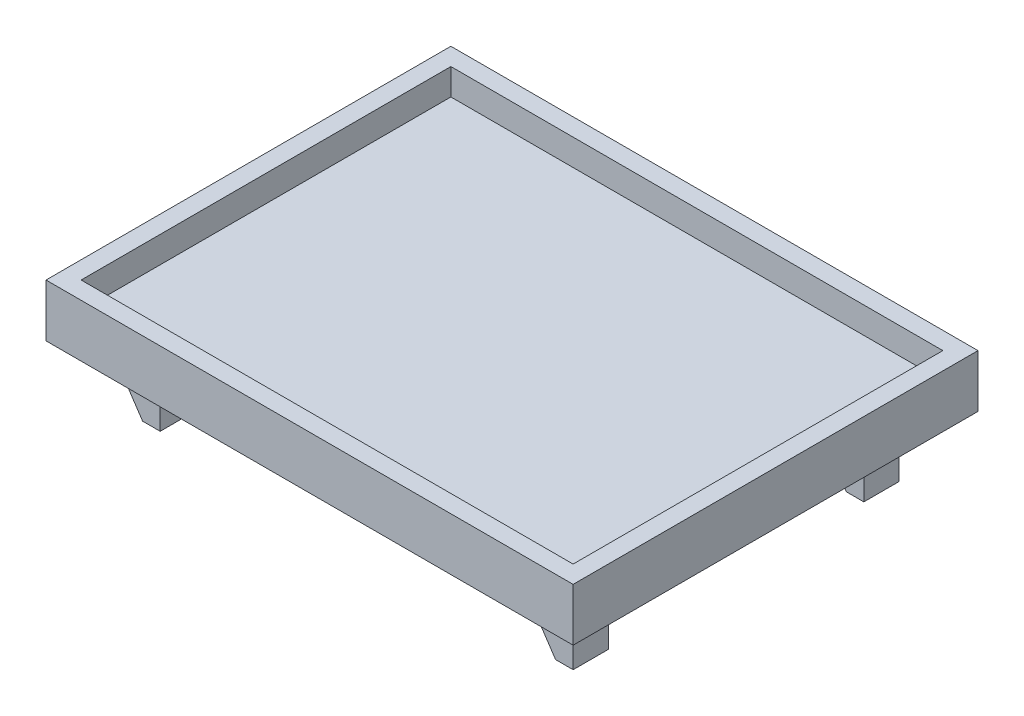
SolidWorks part; units mm, degrees
ref_plane "Front Plane" through (0, 0, 0) normal (0, 0, 1) x (1, 0, 0)
ref_plane "Top Plane" through (0, 0, 0) normal (0, 1, 0) x (1, 0, 0)
ref_plane "Right Plane" through (0, 0, 0) normal (1, 0, 0) x (0, 0, -1)
sketch "Sketch2" plane through (0, 0, 0) normal (0, 1, 0) x (1, 0, 0)
  line L19 (-38.1127, -29.2735) -> (-38.1127, 29.2735)
  line L20 (-35.5727, -26.7335) -> (35.5727, -26.7335) construction
  line L21 (-35.5727, -26.7335) -> (-35.5727, 26.7335) construction
  line L22 (-35.5727, 26.7335) -> (35.5727, 26.7335) construction
  line L23 (35.5727, -26.7335) -> (35.5727, 26.7335) construction
  line L24 (-35.5727, -26.7335) -> (35.5727, 26.7335) construction
  line L25 (-35.5727, 26.7335) -> (35.5727, -26.7335) construction
  line L26 (-38.1127, 29.2735) -> (38.1127, 29.2735)
  line L28 (38.1127, -29.2735) -> (38.1127, 29.2735)
  line L29 (-38.1127, -29.2735) -> (38.1127, -29.2735)
  point P0 (0, 0)
  dimension "D1" = 53.467
  dimension "D2" = 71.1454
  dimension "D3" = 2.54
extrude "Boss-Extrude1" add sketch "Sketch2" against normal blind 7.62
sketch "Sketch3" plane through (0, 0, 0) normal (0, 1, 0) x (1, 0, 0)
  line L24 (-35.5727, -26.7335) -> (35.5727, -26.7335)
  line L25 (35.5727, -26.7335) -> (35.5727, 26.7335)
  line L26 (35.5727, 26.7335) -> (-35.5727, 26.7335)
  line L27 (-35.5727, 26.7335) -> (-35.5727, -26.7335)
  line L32 (-38.1127, -29.2735) -> (38.1127, -29.2735)
  line L33 (38.1127, -29.2735) -> (38.1127, 29.2735)
  line L34 (38.1127, 29.2735) -> (-38.1127, 29.2735)
  line L35 (-38.1127, 29.2735) -> (-38.1127, -29.2735)
  line L36 (-38.1127, -29.2735) -> (38.1127, -29.2735) construction
  line L37 (38.1127, -29.2735) -> (38.1127, 29.2735) construction
  line L38 (38.1127, 29.2735) -> (-38.1127, 29.2735) construction
  line L39 (-38.1127, 29.2735) -> (-38.1127, -29.2735) construction
  dimension "D1" = 0
  dimension "D2" = 2.54
extrude "Cut-Extrude2" cut sketch "Sketch3" against normal blind 3.81
sketch "Sketch4" plane through (0, -7.62, 0) normal (0, -1, 0) x (1, 0, 0)
  line L0 (32.3977, 23.5585) -> (-32.3977, 23.5585) construction
  line L1 (-32.3977, 23.5585) -> (-32.3977, -23.5585) construction
  line L2 (-32.3977, -23.5585) -> (32.3977, -23.5585) construction
  line L3 (32.3977, -23.5585) -> (32.3977, 23.5585) construction
  line L4 (38.1127, 29.2735) -> (-38.1127, 29.2735)
  line L5 (-38.1127, 29.2735) -> (-38.1127, -29.2735)
  line L6 (-38.1127, -29.2735) -> (38.1127, -29.2735)
  line L7 (38.1127, -29.2735) -> (38.1127, 29.2735)
  line L8 (38.1127, 29.2735) -> (-38.1127, 29.2735) construction
  line L9 (-38.1127, 29.2735) -> (-38.1127, -29.2735) construction
  line L10 (-38.1127, -29.2735) -> (38.1127, -29.2735) construction
  line L11 (38.1127, -29.2735) -> (38.1127, 29.2735) construction
  line L12 (-32.3977, 23.5585) -> (-32.3977, 18.4785)
  line L13 (-32.3977, 18.4785) -> (-27.3177, 18.4785)
  line L14 (-27.3177, 18.4785) -> (-27.3177, 23.5585)
  line L15 (-32.3977, 23.5585) -> (-27.3177, 23.5585)
  line L16 (0, -23.5585) -> (0, 23.5585) construction
  line L17 (32.3977, 0) -> (-32.3977, 0) construction
  line L18 (32.3977, 23.5585) -> (32.3977, 18.4785)
  line L19 (32.3977, 18.4785) -> (27.3177, 18.4785)
  line L20 (27.3177, 18.4785) -> (27.3177, 23.5585)
  line L21 (32.3977, 23.5585) -> (27.3177, 23.5585)
  point P15 (0, 0)
  point P19 (0, 0)
  dimension "D3" = 5.08
  dimension "D1" = 0
  dimension "D2" = 5.715
extrude "Boss-Extrude2" add sketch "Sketch4" along normal blind 8.7884
sketch "Sketch5" plane through (0, 0, 23.5585) normal (0, 0, 1) x (1, 0, 0)
  line L0 (-27.3177, -16.4084) -> (-27.3177, -7.62) construction
  line L1 (29.8577, -16.4084) -> (27.3177, -16.4084)
  line L2 (29.8577, -16.4084) -> (27.3177, -12.6069)
  line L3 (-27.3177, -16.4084) -> (-32.3977, -16.4084) construction
  line L4 (-29.8577, -16.4084) -> (-32.3977, -12.6069)
  line L5 (-32.3977, -16.4084) -> (-32.3977, -7.62) construction
  line L6 (27.3177, -7.62) -> (27.3177, -11.3369)
  line L7 (-32.3977, -11.3369) -> (-30.6766, -10.7982)
  line L8 (-30.6766, -10.7982) -> (-30.6766, -7.62)
  line L9 (-27.3177, -7.62) -> (-32.3977, -7.62) construction
  line L10 (-30.6766, -7.62) -> (-32.3977, -7.62)
  line L11 (-32.3977, -7.62) -> (-32.3977, -11.3369)
  line L12 (-29.8577, -16.4084) -> (-32.3977, -16.4084)
  line L13 (-32.3977, -16.4084) -> (-32.3977, -12.6069)
  line L14 (29.0388, -10.7982) -> (29.0388, -7.62)
  line L15 (27.3177, -16.4084) -> (27.3177, -12.6069)
  line L16 (27.3177, -11.3369) -> (29.0388, -10.7982)
  line L17 (29.0388, -7.62) -> (27.3177, -7.62)
  dimension "D1" = 2.54
  dimension "D2" = 4.572
  dimension "D3" = 1.27
  dimension "D4" = 1.8034
  dimension "D5" = 4.572
  dimension "D6" = 1.27
  dimension "D7" = 1.8034
extrude "Cut-Extrude3" cut sketch "Sketch5" against normal up to next (5.08 mm away)
mirror "Mirror1" about plane through (0, 0, 0) normal (0, 0, 1) of "Cut-Extrude3", "Boss-Extrude2"
